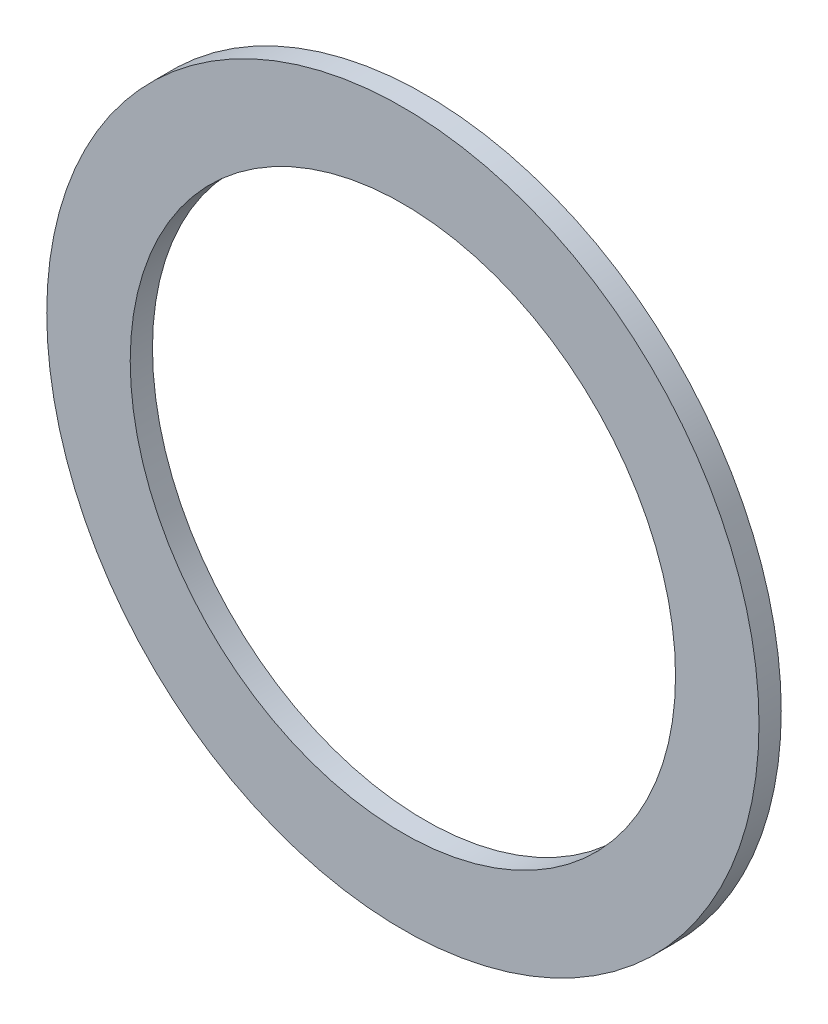
SolidWorks part; units mm, degrees
ref_plane "Front Plane" through (0, 0, 0) normal (0, 0, 1) x (1, 0, 0)
ref_plane "Top Plane" through (0, 0, 0) normal (0, 1, 0) x (1, 0, 0)
ref_plane "Right Plane" through (0, 0, 0) normal (1, 0, 0) x (0, 0, -1)
sketch "Sketch1" plane through (0, 0, 0) normal (0, 0, 1) x (1, 0, 0)
  circle A0 centre (0, 0) radius 12.25
  circle A1 centre (0, 0) radius 16
  dimension "D1" = 32
  dimension "D2" = 24.5
extrude "Boss-Extrude1" add sketch "Sketch1" along normal blind 1
